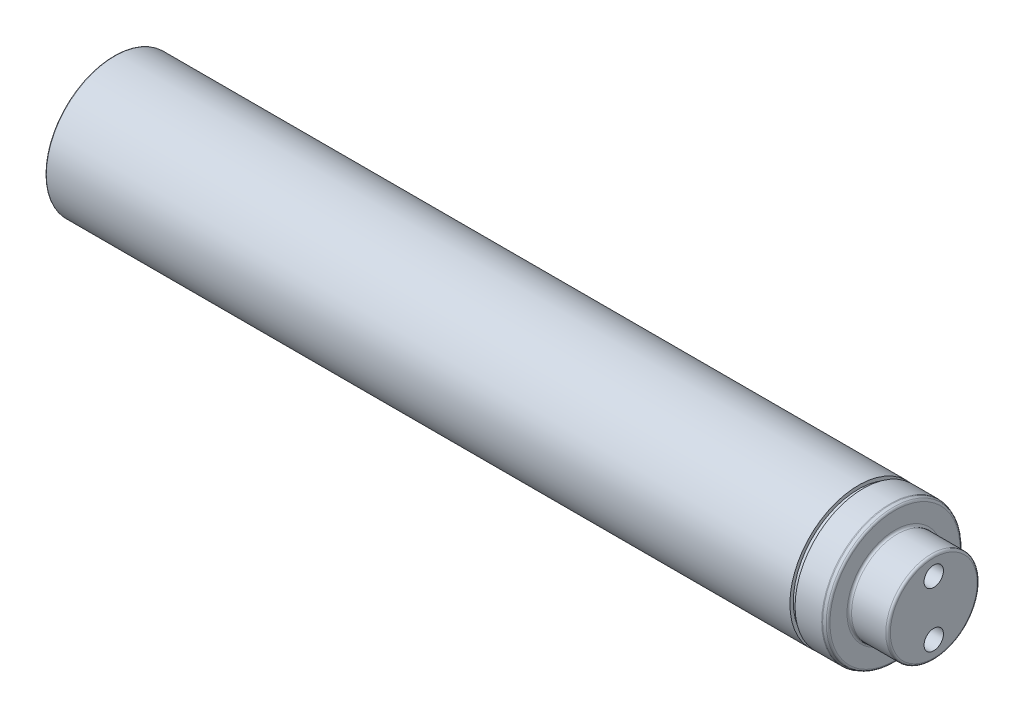
SolidWorks part; units mm, degrees
revolve "Base-Revolve" add sketch "Sketch1" angle 360 about L0
sketch "Sketch1" plane through (0, 0, 0) normal (0, 0, 1) x (1, 0, 0)
  line L0 (-168, 0) -> (195.05, 0) construction
  line L1 (163, 30) -> (0, 30)
  line L2 (163, 30) -> (163, 28.5)
  line L4 (-145.0555, 0) -> (196, 0)
  line L5 (178.342, 29.4115) -> (177.1657, 29.8397)
  line L6 (-163, 29.6) -> (-163, 28.4)
  line L7 (-168, 5.1) -> (-148, 5.1)
  line L8 (-148, 5.1) -> (-145.0555, 0)
  line L9 (180, 20) -> (195, 20)
  line L10 (196, 19) -> (196, 0)
  line L13 (0, 30) -> (-162.6, 30)
  line L17 (-164.2, 24.8845) -> (-167.8, 22.8061)
  line L19 (-164, 28) -> (-164, 25.2309)
  line L20 (-168, 22.4597) -> (-168, 5.1)
  line L21 (-163.4, 28) -> (-164, 28)
  line L22 (179, 28.4719) -> (179, 21)
  line L23 (165.15, 29.9) -> (176.8237, 29.9)
  line L24 (165.15, 28.5) -> (165.15, 29.9)
  line L25 (163, 28.5) -> (165.15, 28.5)
  arc A0 (179, 28.4719) -> (178.342, 29.4115) centre (178, 28.4719) ccw
  arc A1 (-163.4, 28) -> (-163, 28.4) centre (-163.4, 28.4) ccw
  arc A2 (176.8237, 29.9) -> (177.1657, 29.8397) centre (176.8237, 28.9) cw
  arc A3 (-167.8, 22.8061) -> (-168, 22.4597) centre (-167.6, 22.4597) ccw
  arc A4 (-164.2, 24.8845) -> (-164, 25.2309) centre (-164.4, 25.2309) ccw
  arc A5 (-163, 29.6) -> (-162.6, 30) centre (-162.6, 29.6) cw
  arc A6 (180, 20) -> (179, 21) centre (180, 21) cw
  arc A7 (195, 20) -> (196, 19) centre (195, 19) cw
  point P15 (177, 29.9)
  point P28 (-164, 25)
  point P31 (-163, 30)
  dimension "D11" = 50
  dimension "D6" = 2
  dimension "D15" = 40
  dimension "D16" = 20
  dimension "D17" = 1
  dimension "D18" = 17
  dimension "D19" = 0.4
  dimension "D23" = 1
  dimension "D2" = 59.8
  dimension "D3" = 57
  dimension "D4" = 2.15
  dimension "D5" = 16
  dimension "D7" = 5
  dimension "D8" = 1
  dimension "D9" = 56
  dimension "D10" = 30
  dimension "D12" = 60
  dimension "D13" = 163
  dimension "D14" = 326
  dimension "D20" = 10.2
  dimension "D21" = 20
  dimension "D22" = 60
  dimension "D24" = 364
cosmetic thread "Cosmetic Thread1"
ref_plane "Front" through (0, 0, 0) normal (0, 0, 1) x (1, 0, 0)
ref_plane "Top" through (0, 0, 0) normal (0, 1, 0) x (1, 0, 0)
ref_plane "Right" through (0, 0, 0) normal (1, 0, 0) x (0, 0, -1)
hole_wizard "Hole2" positions "Sketch4" profile "Sketch3" legacy
sketch "Sketch4" plane through (196, 0, 0) normal (1, 0, 0) x (0, 0, -1)
  line L0 (0, 0) -> (-13.5802, 0) construction
  line L1 (0, 0) -> (0, 12) construction
  point P0 (0, 12)
  point P6 (0, -12)
  dimension "D1" = 24
sketch "Sketch3" plane through (196, 12, 0) normal (0, 1, 0) x (0, 0, -1)
  line L0 (0, 0) -> (0, 22.5537)
  line L1 (0, 22.5537) -> (4.25, 20)
  line L2 (4.25, 20) -> (4.25, 0)
  line L4 (4.25, 0) -> (0, 0)
  line L6 (0, 22.5537) -> (-4.25, 20) construction
  line L7 (0, -4.2442) -> (0, 117.3081) construction
  dimension "Diameter" = 8.5
  dimension "Depth" = 20
  dimension "Drill Angle" = 118
cosmetic thread "Cosmetic Thread3"
cosmetic thread "Cosmetic Thread4"
